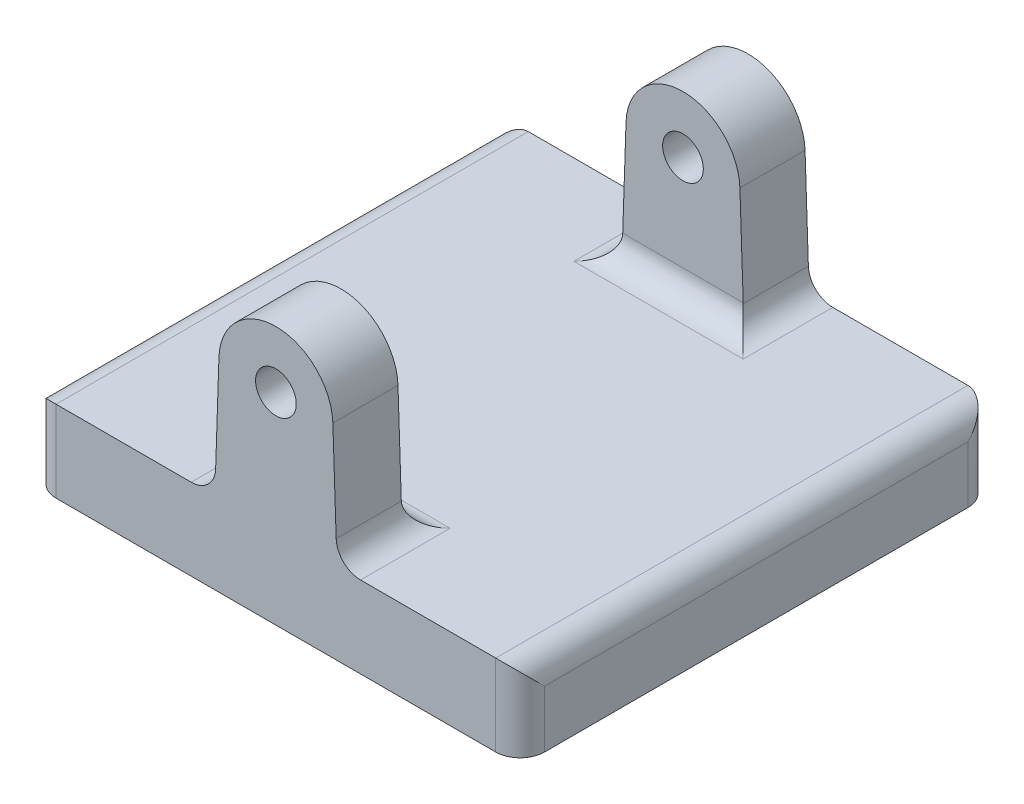
SolidWorks part; units mm, degrees
ref_plane "Front Plane" through (0, 0, 0) normal (0, 0, 1) x (1, 0, 0)
ref_plane "Top Plane" through (0, 0, 0) normal (0, 1, 0) x (1, 0, 0)
ref_plane "Right Plane" through (0, 0, 0) normal (1, 0, 0) x (0, 0, -1)
sketch "Sketch2" plane through (0, 0, 0) normal (0, 1, 0) x (1, 0, 0)
  line L1 (-30, -29) -> (30, -29)
  line L2 (-30, -29) -> (-30, 29)
  line L3 (-30, 29) -> (30, 29)
  line L4 (30, -29) -> (30, 29)
  line L5 (-30, -29) -> (30, 29) construction
  line L6 (-30, 29) -> (30, -29) construction
  point P0 (0, 0)
  dimension "D1" = 58
  dimension "D2" = 60
extrude "Boss-Extrude1" add sketch "Sketch2" along normal blind 10
sketch "Sketch3" plane through (0, 0, 29) normal (0, 0, 1) x (1, 0, 0)
  line L0 (-7.5, 10) -> (-6.9961, 25)
  line L1 (-30, 10) -> (30, 10) construction
  line L2 (6.9961, 25) -> (7.5, 10)
  line L3 (-7.5, 10) -> (7.5, 10)
  arc A0 (-6.9961, 25) -> (6.9961, 25) centre (0, 24.765) cw
  circle A1 centre (0, 24.765) radius 2.5
  dimension "D1" = 7
  dimension "D4" = 5
  dimension "D2" = 15
  dimension "D3" = 15
extrude "Boss-Extrude2" add sketch "Sketch3" against normal blind 8
mirror "Mirror1" about plane through (0, 0, 0) normal (0, 0, 1) of "Boss-Extrude2"
fillet "Fillet1" radius 3 12 edges at (7.5, 10, -25) (7.5, 10, 25) (-7.5, 10, 25) (-7.5, 10, -25) (30, 10, 0) (0, 10, 21) (-30, 10, 0) (0, 10, -21) (30, 5, 29) (-30, 5, 29) (-30, 5, -29) (30, 5, -29)
